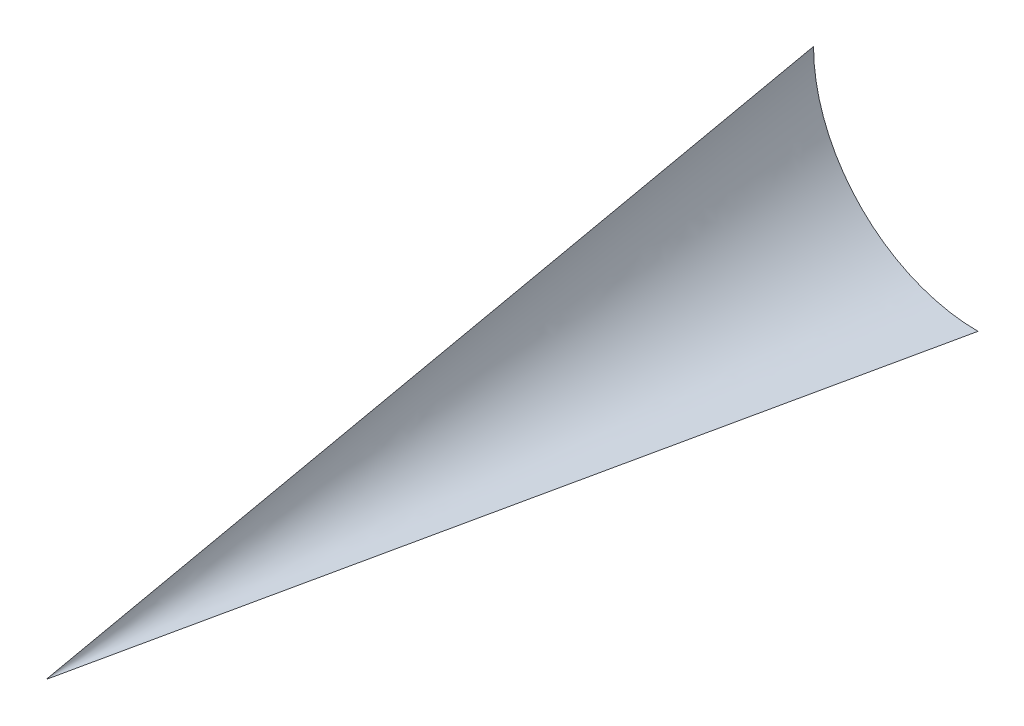
SolidWorks part; units mm, degrees
ref_plane "Plan de face" through (0, 0, 0) normal (0, 0, 1) x (1, 0, 0)
ref_plane "Plan de dessus" through (0, 0, 0) normal (0, 1, 0) x (1, 0, 0)
ref_plane "Plan de droite" through (0, 0, 0) normal (1, 0, 0) x (0, 0, -1)
sketch "Esquisse1" plane through (0, 0, 0) normal (0, 0, 1) x (1, 0, 0)
  line L0 (0, 15) -> (0, 0)
  line L1 (0, 0) -> (15, 0)
  arc A0 (0, 15) -> (15, 0) centre (15, 15) ccw
  dimension "D1" = 15
sketch "Esquisse2" plane through (0, 0, 0) normal (0, 1, 0) x (1, 0, 0)
  point P0 (0, -70)
  dimension "D1" = 70
loft "Lissage1" add profiles "Esquisse2", "Esquisse1"
